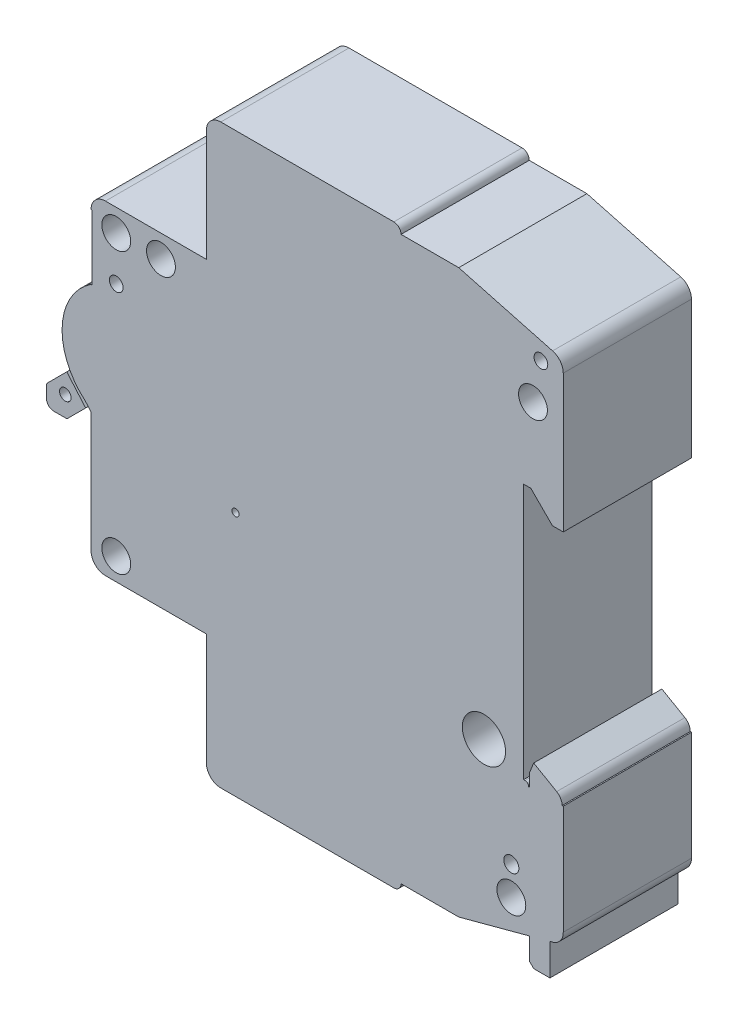
SolidWorks part; units mm, degrees
ref_plane "Front Plane" through (0, 0, 0) normal (0, 0, 1) x (1, 0, 0)
ref_plane "Top Plane" through (0, 0, 0) normal (0, 1, 0) x (1, 0, 0)
ref_plane "Right Plane" through (0, 0, 0) normal (1, 0, 0) x (0, 0, -1)
sketch "Sketch1" plane through (0, 0, 0) normal (0, 0, 1) x (1, 0, 0)
  line L0 (35.5, 14.5) -> (34, 14.5)
  line L1 (34, 14.5) -> (31, 17.5)
  line L2 (31, 17.5) -> (30, 17.5)
  line L3 (30, 17.5) -> (30, -18)
  line L5 (30.7, -18.5) -> (30.8, -18.5)
  line L6 (30.8, -18.5) -> (30.8, -16.8)
  line L7 (30.8, -16.8) -> (31.4, -15.3)
  line L8 (31.4, -15.3) -> (34.5875, -17.1403)
  line L10 (35.3375, -18.4393) -> (35.5, -18.4393)
  line L11 (35.5, -18.4393) -> (35.5, -33.5801)
  line L12 (33.6855, -35.5715) -> (33.65, -35.6104)
  line L13 (33.65, -35.6104) -> (33.65, -40)
  line L14 (33.65, -40) -> (31.4, -40)
  line L15 (31.4, -40) -> (30.8, -39.4)
  line L16 (30.8, -39.4) -> (30.8, -36.3741)
  line L17 (30.8, -36.3741) -> (21, -39)
  line L18 (21, -39) -> (13, -39)
  line L20 (12, -40) -> (-12, -40)
  line L22 (-14, -38) -> (-14, -22.5)
  line L23 (-14, -22.5) -> (-28, -22.5)
  line L24 (-30.8603, -2.8306) -> (-32.6191, -0.7906)
  line L25 (-30, -20.5) -> (-30, -3.8284)
  line L26 (-30.8603, -2.8306) -> (-30, -3.8284)
  line L27 (-30, 11.4833) -> (-29.873, 11.4833)
  line L28 (-29.873, 11.4833) -> (-29.873, 20.5)
  line L29 (-29.873, 20.5) -> (-30, 20.5)
  line L31 (-28, 22.5) -> (-14, 22.5)
  line L32 (-14, 22.5) -> (-14, 38)
  line L34 (-12, 40) -> (12, 40)
  line L36 (13, 39) -> (21, 39)
  line L37 (21, 39) -> (34.0176, 35.5125)
  line L39 (35.5, 33.5806) -> (35.5, 14.5)
  line L40 (30.2, -18) -> (30, -18)
  arc A1 (-12, 40) -> (-14, 38) centre (-12, 38) ccw
  arc A2 (13, 39) -> (12, 40) centre (12, 39) ccw
  circle A3 centre (32.4, 33.5) radius 0.95
  arc A4 (35.5, 33.5806) -> (34.0176, 35.5125) centre (33.5, 33.5806) ccw
  circle A5 centre (31.3, 28) radius 2
  arc A7 (30.7, -18.5) -> (30.2, -18) centre (30.2, -18.5) ccw
  arc A8 (35.3375, -18.4393) -> (34.5875, -17.1403) centre (33.8375, -18.4393) ccw
  circle A9 centre (24.5, -15.9) radius 3
  circle A10 centre (28.2973, -29) radius 1.0479
  circle A11 centre (28.2973, -33) radius 2
  arc A12 (33.6855, -35.5715) -> (35.5, -33.5801) centre (33.5, -33.5801) ccw
  arc A13 (12, -40) -> (13, -39) centre (12, -39) ccw
  arc A14 (-14, -38) -> (-12, -40) centre (-12, -38) ccw
  circle A15 centre (-26.5, -19.4) radius 2
  arc A16 (-30, -20.5) -> (-28, -22.5) centre (-28, -20.5) ccw
  circle A17 centre (-9.9586, -5.8923) radius 0.495
  arc A18 (-30, 11.4833) -> (-32.6191, -0.7906) centre (-25, 4) ccw
  circle A19 centre (-32.65, 4) radius 0.65
  circle A20 centre (-26.5, 13.3) radius 0.95
  circle A21 centre (-26.5, 19.4) radius 2
  circle A22 centre (-20.3, 19.4) radius 2
  arc A23 (-28, 22.5) -> (-30, 20.5) centre (-28, 20.5) ccw
  dimension "D1" = 4
  dimension "D2" = 4
  dimension "D3" = 1.9
  dimension "D4" = 1.3
  dimension "D5" = 0.99
  dimension "D6" = 4
  dimension "D7" = 4
  dimension "D8" = 2.0959
  dimension "D9" = 6
  dimension "D10" = 4
  dimension "D13" = 1.9
  dimension "D17" = 2
  dimension "D19" = 1
  dimension "D20" = 2
  dimension "D23" = 2
  dimension "D26" = 9
  dimension "D28" = 2
  dimension "D31" = 2
  dimension "D33" = 1
  dimension "D42" = 2
  dimension "D45" = 1.5
  dimension "D52" = 0.5
  dimension "D11" = 1.3175
  dimension "D12" = 2.6935
  dimension "D14" = 24
  dimension "D15" = 8
  dimension "D16" = 13.4766
  dimension "D18" = 19.0806
  dimension "D21" = 15.5
  dimension "D22" = 14
  dimension "D24" = 0.127
  dimension "D25" = 9.0167
  dimension "D27" = 16.6716
  dimension "D29" = 14
  dimension "D30" = 15.5
  dimension "D32" = 24
  dimension "D34" = 8
  dimension "D35" = 10.1457
  dimension "D36" = 3.0259
  dimension "D37" = 75
  dimension "D38" = 0.8485
  dimension "D39" = 135
  dimension "D40" = 2.25
  dimension "D41" = 4.3896
  dimension "D43" = 15.1407
  dimension "D44" = 0.1625
  dimension "D46" = 3.6806
  dimension "D47" = 1.6155
  dimension "D48" = 120
  dimension "D49" = 158.199
  dimension "D50" = 1.7
  dimension "D51" = 0.1
  dimension "D53" = 0.2
  dimension "D54" = 35.5
  dimension "D55" = 1
  dimension "D56" = 4.2426
  dimension "D57" = 1.5
extrude "Boss-Extrude1" add sketch "Sketch1" along normal blind 17.78
sketch "Sketch2" plane through (0, 0, 17.78) normal (0, 0, 1) x (1, 0, 0)
  line L0 (-25, 4) -> (-30.795, -2.9063) construction
  line L1 (-30.7851, 10.8944) -> (-25, 4) construction
  line L2 (-32.6191, -0.7906) -> (-30, -3.8284) construction
  line L3 (-25, 4) -> (-31.5, 4) construction
  line L4 (-31.4279, 11.6604) -> (-29.1781, 8.9793)
  line L7 (-29.1781, -0.9793) -> (-31.4279, -3.6604)
  arc A0 (-29.1781, 8.9793) -> (-29.1781, -0.9793) centre (-25, 4) ccw
  arc A1 (-30, 11.4833) -> (-32.6191, -0.7906) centre (-25, 4) ccw construction
  arc A2 (-31.4279, 11.6604) -> (-31.4279, -3.6604) centre (-25, 4) ccw
  dimension "D1" = 13
  dimension "D4" = 20
  dimension "D2" = 50
  dimension "D3" = 50
extrude "Cut-Extrude1" cut sketch "Sketch2" against normal blind 14.78
sketch "Sketch3" plane through (0, 0, 17.78) normal (0, 0, 1) x (1, 0, 0)
  line L0 (-29.1781, 8.9793) -> (-30.7851, 10.8944) construction
  line L1 (-29.1781, -0.9793) -> (-30.795, -2.9063)
  line L4 (-30.795, 10.9063) -> (-29.1781, 8.9793)
  line L7 (-30.795, -2.9063) -> (-29.1781, -0.9793) construction
  arc A0 (-29.1781, 8.9793) -> (-29.1781, -0.9793) centre (-25, 4) ccw
  arc A1 (-30.795, 10.9063) -> (-30.795, -2.9063) centre (-25, 4) ccw
extrude "Boss-Extrude2" add sketch "Sketch3" against normal blind 3
sketch "Sketch4" plane through (-19.102, -16.4689, 0) normal (-0.7574, -0.653, 0) x (0, 0, 1)
  line L1 (3.5, 20.2007) -> (14.28, 20.2007)
  line L2 (3.5, 20.2007) -> (3.5, 18.3109)
  line L3 (3.5, 18.3109) -> (14.28, 18.3109)
  line L4 (14.28, 20.2007) -> (14.28, 18.3109)
  line L5 (3, 20.7007) -> (3, 17.9073) construction
  line L6 (14.78, 28.3694) -> (14.78, 17.9073) construction
  line L7 (3, 18.3109) -> (14.78, 18.3109) construction
  line L8 (3, 20.7007) -> (0, 20.7007) construction
  point P6 (1.5, 20.7007)
  dimension "D1" = 0.5
  dimension "D2" = 0.5
  dimension "D3" = 0.5
extrude "Cut-Extrude2" cut sketch "Sketch4" against normal blind 2.5
sketch "Sketch5" plane through (-17.2086, -14.8364, 0) normal (-0.7574, -0.653, 0) x (0, 0, 1)
  line L1 (3.5, 20.2007) -> (14.28, 20.2007)
  line L2 (3.5, 20.2007) -> (3.5, 18.3109)
  line L3 (3.5, 18.3109) -> (14.28, 18.3109)
  line L4 (14.28, 20.2007) -> (14.28, 18.3109)
extrude "Boss-Extrude3" add sketch "Sketch5" along normal blind 3
sketch "Sketch6" plane through (0, 0, 0) normal (0, 0, 1) x (1, 0, 0)
  line L0 (-33.3638, -0.6925) -> (-30.7448, -3.7303)
  line L1 (-30.7448, -3.7303) -> (-33.1865, -6.1721)
  line L3 (-33.5373, -6.3185) -> (-35.1648, -6.3274)
  line L4 (-31.4373, -2.927) -> (-32.6713, -1.4958) construction
  line L5 (-36.1703, -5.322) -> (-36.1614, -3.6945)
  line L6 (-32.0543, -2.2114) -> (-33.569, -3.5174) construction
  line L7 (-36.0149, -3.3437) -> (-33.3638, -0.6925)
  arc A0 (-36.1703, -5.322) -> (-35.1648, -6.3274) centre (-35.1703, -5.3275) ccw
  arc A1 (-36.0149, -3.3437) -> (-36.1614, -3.6945) centre (-35.6614, -3.6972) ccw
  arc A2 (-33.5373, -6.3185) -> (-33.1865, -6.1721) centre (-33.5401, -5.8185) ccw
  circle A3 centre (-33.569, -3.5174) radius 0.8
  point P6 (-32.0543, -2.2114)
  point P8 (-32.0543, -2.2114)
  dimension "D1" = 1.6
  dimension "D2" = 2
extrude "Boss-Extrude4" add sketch "Sketch6" along normal up to surface (17.78 mm away) up to face at (8.8717, -5.0648, 17.78)
